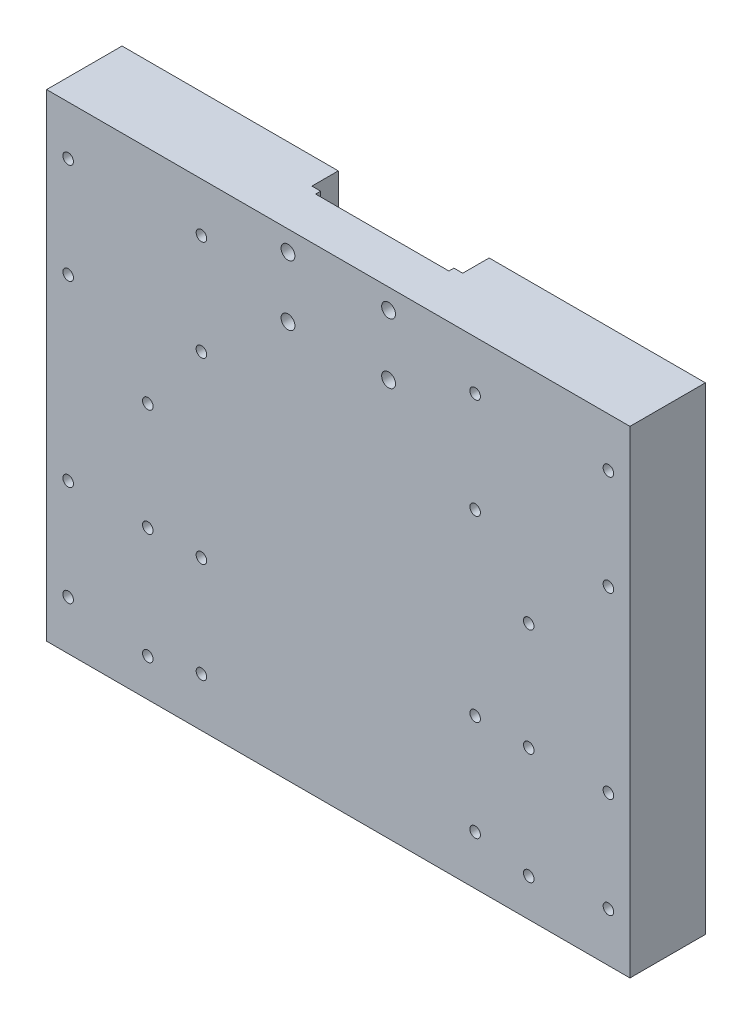
SolidWorks part; units mm, degrees
ref_plane "Piano frontale" through (0, 0, 0) normal (0, 0, 1) x (1, 0, 0)
ref_plane "Piano superiore" through (0, 0, 0) normal (0, 1, 0) x (1, 0, 0)
ref_plane "Piano destro" through (0, 0, 0) normal (1, 0, 0) x (0, 0, -1)
sketch "Schizzo1" plane through (0, 0, 0) normal (0, 0, 1) x (1, 0, 0)
  line L1 (116, -95) -> (-116, -95)
  line L2 (116, -95) -> (116, 95)
  line L3 (116, 95) -> (-116, 95)
  line L4 (-116, -95) -> (-116, 95)
  line L5 (116, -95) -> (-116, 95) construction
  line L6 (116, 95) -> (-116, -95) construction
  point P0 (0, 0)
  dimension "D1" = 232
  dimension "D2" = 190
extrude "Estrusione-Estrusione1" add sketch "Schizzo1" along normal blind 30
sketch "Schizzo3" plane through (0, 0, 30) normal (0, 0, 1) x (1, 0, 0)
  line L0 (20, 7) -> (-20, 7) construction
  line L1 (-20, 7) -> (20, -17) construction
  line L2 (20, -17) -> (20, 7) construction
  line L3 (20, 7) -> (-20, -17) construction
  line L4 (-20, -17) -> (-20, 7) construction
  line L5 (-20, -17) -> (20, -17) construction
  circle A8 centre (20, 7) radius 3
  circle A9 centre (-20, 7) radius 3
  circle A10 centre (-20, -17) radius 3
  circle A11 centre (20, -17) radius 3
  point P21 (0, -5)
  dimension "D1" = 40
  dimension "D2" = 24
sketch "Schizzo4" plane through (0, 95, 0) normal (0, 1, 0) x (1, 0, 0)
  line L0 (116, 0) -> (-116, 0) construction
  line L1 (30, 0) -> (-30, 0)
  line L2 (30, 0) -> (30, -10.5)
  line L3 (30, -10.5) -> (-30, -10.5)
  line L4 (-30, 0) -> (-30, -10.5)
  dimension "D1" = 10.5
extrude "Taglio-Estrusione2" cut sketch "Schizzo4" against normal through all
sketch "Sketch1" plane through (0, 0, 0) normal (0, 0, -1) x (-1, 0, 0)
  line L0 (-52.5, 88.5) -> (-109.5, 88.5) construction
  line L1 (-81, 88.5) -> (-80, -95) construction
  point P0 (-109.5, 88.5)
  point P1 (-109.5, 43.5)
  point P3 (-52.5, 88.5)
  point P5 (-52.5, 43.5)
  point P7 (-52.5, -43.5)
  point P9 (-109.5, -43.5)
  point P11 (-109.5, -88.5)
  point P13 (-52.5, -88.5)
  point P15 (52.5, -88.5)
  point P17 (109.5, -88.5)
  point P19 (109.5, -43.5)
  point P21 (52.5, -43.5)
  point P23 (52.5, 43.5)
  point P25 (109.5, 43.5)
  point P27 (109.5, 88.5)
  point P29 (52.5, 88.5)
hole_wizard "Tap Drill for M5 Tap1" positions "Sketch2" profile "Sketch3" hole size "M5" standard "ISO" end condition through all
sketch "Sketch2" plane through (0, 0, 0) normal (0, 0, -1) x (-1, 0, 0)
  line L3 (0, 95) -> (0, -95) construction
  line L4 (-116, 95) -> (116, 95) construction
  line L5 (116, -95) -> (-116, -95) construction
  line L7 (116, 0) -> (-116, 0) construction
  line L8 (116, 95) -> (116, -95) construction
  line L9 (-116, -95) -> (-116, 95) construction
  line L13 (-54.4288, 75.5) -> (-107.4288, 75.5)
  line L14 (-54.4288, 75.5) -> (-54.4288, 35.5)
  line L15 (-54.4288, 35.5) -> (-107.4288, 35.5)
  line L16 (-107.4288, 75.5) -> (-107.4288, 35.5)
  line L18 (-107.4288, -35.5) -> (-54.4288, -35.5)
  line L19 (-107.4288, -35.5) -> (-107.4288, -75.5)
  line L20 (-107.4288, -75.5) -> (-54.4288, -75.5)
  line L21 (-54.4288, -35.5) -> (-54.4288, -75.5)
  point P72 (-54.4288, 75.5)
  point P76 (-107.4288, 35.5)
  point P681 (-107.4288, -75.5)
  point P682 (-107.4288, -35.5)
  point P683 (-54.4288, -35.5)
  point P684 (-54.4288, -75.5)
  point P685 (54.4288, -75.5)
  point P686 (54.4288, -35.5)
  point P687 (107.4288, -35.5)
  point P688 (107.4288, -75.5)
  point P689 (107.4288, 75.5)
  point P690 (107.4288, 35.5)
  point P691 (54.4288, 35.5)
  point P692 (54.4288, 75.5)
  point P695 (-107.4288, 75.5)
  point P699 (-54.4288, 35.5)
  dimension "D1" = 53
  dimension "D2" = 40
sketch "Sketch3" plane through (54.4288, 35.5, 0) normal (1, 0, 0) x (0, 1, 0)
  line L0 (0, 0) -> (0, 30)
  line L1 (0, 30) -> (2.1, 30)
  line L2 (2.1, 30) -> (2.1, 0)
  line L5 (2.1, 0) -> (0, 0)
  line L11 (0, -6.35) -> (0, 107.95) construction
  dimension "Thru Hole Dia." = 4.2
  dimension "Thru Hole Depth" = 30
hole_wizard "M5 Clearance Hole1" positions "Sketch4" profile "Sketch5" hole size "M5" standard "ISO" end condition through all
sketch "Sketch4" plane through (0, 0, 30) normal (0, 0, 1) x (1, 0, 0)
  point P0 (-20, 87)
  point P3 (20, 87)
  point P6 (20, 63)
  point P9 (-20, 63)
sketch "Sketch5" plane through (-20, 87, 30) normal (1, 0, 0) x (0, -1, 0)
  line L0 (0, 0) -> (0, 30)
  line L1 (0, 30) -> (2.75, 30)
  line L2 (2.75, 30) -> (2.75, 0)
  line L5 (2.75, 0) -> (0, 0)
  line L11 (0, -6.35) -> (0, 107.95) construction
  dimension "Thru Hole Dia." = 5.5
  dimension "Thru Hole Depth" = 30
hole_wizard "Tap Drill for M5 Tap3" positions "Sketch6" profile "Sketch7" hole size "M5" standard "ISO" end condition up to next
sketch "Sketch6" plane through (0, 0, 30) normal (0, 0, 1) x (1, 0, 0)
  point P0 (-75.75, 7)
  point P6 (-75.75, -80)
  point P8 (75.75, 7)
  point P14 (75.75, -80)
  point P23 (-75.75, -35.7925)
  point P25 (75.75, -35.7925)
sketch "Sketch7" plane through (-75.75, 7, 30) normal (1, 0, 0) x (0, -1, 0)
  line L0 (0, 0) -> (0, 30)
  line L1 (0, 30) -> (2.1, 30)
  line L2 (2.1, 30) -> (2.1, 0)
  line L5 (2.1, 0) -> (0, 0)
  line L11 (0, -6.35) -> (0, 107.95) construction
  dimension "Thru Hole Dia." = 4.2
  dimension "Thru Hole Depth" = 30
sketch "Sketch8" plane through (0, 0, 10.5) normal (0, 0, -1) x (-1, 0, 0)
  line L0 (30, 95) -> (-30, 95) construction
  line L1 (-26.5, 95) -> (26.5, 95)
  line L2 (-26.5, 95) -> (-26.5, 43)
  line L3 (-26.5, 43) -> (26.5, 43)
  line L4 (26.5, 95) -> (26.5, 43)
  line L5 (-30, 78.9991) -> (30, 78.9991) construction
  line L6 (-30, -95) -> (-30, 95) construction
  line L7 (30, -95) -> (30, 95) construction
  line L8 (0, 78.9991) -> (0, 101.437) construction
  dimension "D1" = 26.5
  dimension "D2" = 26.5
  dimension "D3" = 52
extrude "Cut-Extrude1" cut sketch "Sketch8" against normal blind 2
